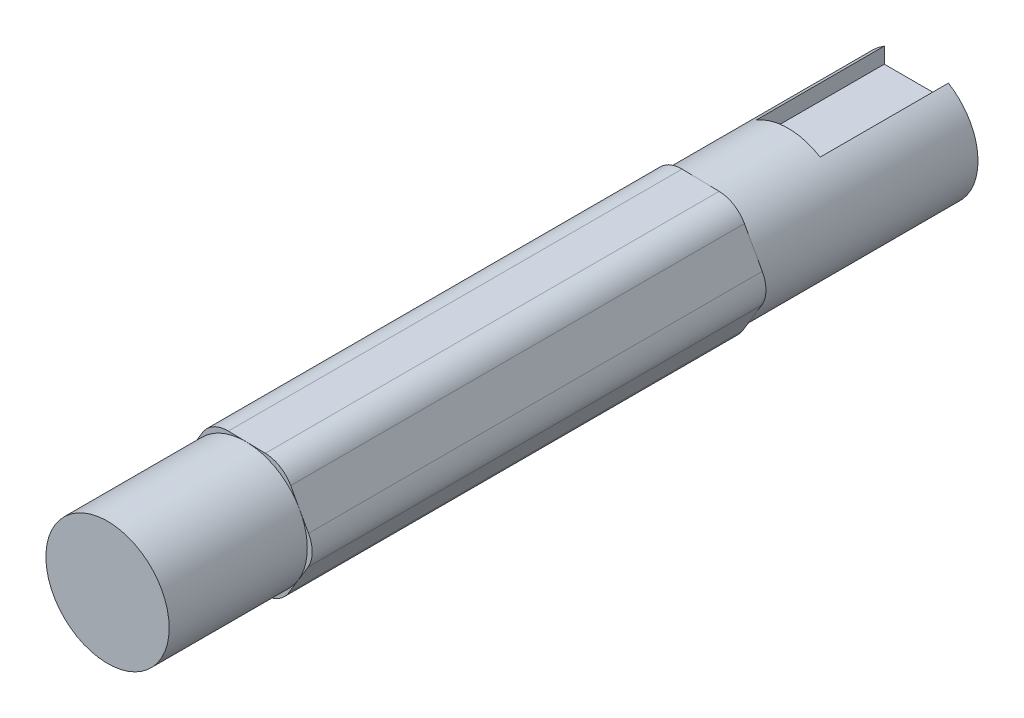
SolidWorks part; units mm, degrees
ref_plane "Front Plane" through (0, 0, 0) normal (0, 0, 1) x (1, 0, 0)
ref_plane "Top Plane" through (0, 0, 0) normal (0, 1, 0) x (1, 0, 0)
ref_plane "Right Plane" through (0, 0, 0) normal (1, 0, 0) x (0, 0, -1)
sketch "Sketch1" plane through (0, 0, 0) normal (0, 0, 1) x (1, 0, 0)
  circle A0 centre (0, 0) radius 6.25
  dimension "D1" = 12.5
extrude "Boss-Extrude1" add sketch "Sketch1" along normal blind 37 and the other way blind 45
sketch "Sketch3" plane through (0, 0, 0) normal (0, 1, 0) x (1, 0, 0)
  line L0 (-27.349, 0) -> (27.9883, 0) construction
  line L1 (-27.349, 31) -> (27.9883, 31) construction
  line L2 (-27.349, 32) -> (27.9883, 32) construction
  line L3 (-27.349, 42) -> (27.9883, 42) construction
  line L4 (27.9883, 45) -> (-27.349, 45) construction
  line L5 (-27.349, -31) -> (27.9883, -31) construction
  line L6 (-27.349, -37) -> (27.9883, -37) construction
  dimension "D1" = 31
  dimension "D2" = 1
  dimension "D3" = 10
  dimension "D4" = 3
  dimension "D5" = 31
  dimension "D6" = 6
sketch "Sketch4" plane through (0, 0, -45) normal (0, 0, -1) x (-1, 0, 0)
  line L0 (-18.2857, 6.25) -> (18.9059, 6.25) construction
  line L1 (-3.25, 8.75) -> (3.25, 8.75)
  line L2 (-3.25, 8.75) -> (-3.25, 3.75)
  line L3 (-3.25, 3.75) -> (3.25, 3.75)
  line L4 (3.25, 8.75) -> (3.25, 3.75)
  line L5 (0, 15.7597) -> (0, -12.3933) construction
  circle A0 centre (0, 0) radius 6.25 construction
  dimension "D1" = 6.5
  dimension "D2" = 5
extrude "Cut-Extrude1" cut sketch "Sketch4" against normal blind 13
ref_plane "Plane1" through (0, 0, 23) normal (0, 0, 1) x (1, 0, 0)
ref_plane "Plane2" through (0, 0, -23) normal (0, 0, 1) x (1, 0, 0)
sketch "Sketch5" plane through (0, 0, -23) normal (0, 0, 1) x (1, 0, 0)
  line L1 (3.7329, 6.1765) -> (-3.4825, 6.321)
  line L2 (-3.4825, 6.321) -> (-7.2154, 0.1445)
  line L3 (-7.2154, 0.1445) -> (-3.7329, -6.1765)
  line L4 (-3.7329, -6.1765) -> (3.4825, -6.321)
  line L5 (3.4825, -6.321) -> (7.2154, -0.1445)
  line L6 (7.2154, -0.1445) -> (3.7329, 6.1765)
  circle A0 centre (0, 0) radius 6.25 construction
  dimension "D1" = 12.5
extrude "Boss-Extrude2" add sketch "Sketch5" along normal up to surface (46 mm away) up to plane "Plane1"
fillet "Fillet1" radius 3 6 edges at (-3.4825, 6.321, 0) (-7.2154, 0.1445, 0) (-3.7329, -6.1765, 0) (3.4825, -6.321, 0) (7.2154, -0.1445, 0) (3.7329, 6.1765, 0)
